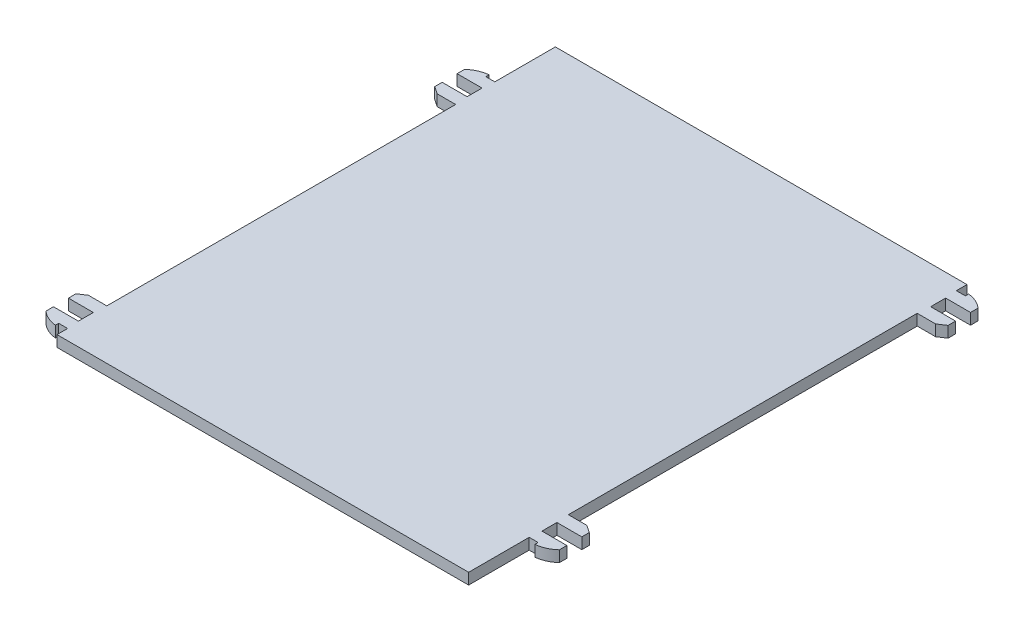
SolidWorks part; units mm, degrees
ref_plane "Front" through (0, 0, 0) normal (0, 0, 1) x (1, 0, 0)
ref_plane "Top" through (0, 0, 0) normal (0, 1, 0) x (1, 0, 0)
ref_plane "Right" through (0, 0, 0) normal (1, 0, 0) x (0, 0, -1)
sketch "Sketch1" plane through (0, 0, 0) normal (0, 1, 0) x (1, 0, 0)
  line L0 (43.1, 45.51) -> (46.5, 45.51)
  line L1 (-41.3, 50) -> (41.3, 50)
  line L2 (-41.3, 50) -> (-41.3, -50)
  line L3 (-41.3, -50) -> (41.3, -50)
  line L4 (41.3, 50) -> (41.3, -50)
  line L5 (-41.3, 50) -> (41.3, -50) construction
  line L6 (-41.3, -50) -> (41.3, 50) construction
  line L7 (41.3, 47.87) -> (43.1, 47.87)
  line L8 (41.3, 47.87) -> (41.3, 45.51)
  line L9 (41.3, 45.51) -> (43.1, 45.51)
  line L10 (43.1, 47.87) -> (43.1, 45.51)
  line L11 (46.5, 45.51) -> (46.5, 47.01)
  line L12 (43.1, 47.87) -> (43.1, 48.52)
  line L13 (41.3, 45.51) -> (41.5, 45.51)
  line L14 (41.3, 45.51) -> (41.3, 42.51)
  line L15 (41.3, 42.51) -> (41.5, 42.51)
  line L16 (41.5, 45.51) -> (41.5, 42.51)
  line L17 (41.5, 42.51) -> (46.5, 42.51)
  line L18 (46.5, 42.51) -> (46.5, 41.01)
  line L19 (46.5, 41.01) -> (45, 40.01)
  line L20 (45, 40.01) -> (41.3, 40.01)
  line L21 (41.3, 5.01) -> (60.4529, 5.01) construction
  line L22 (41.5, -32.49) -> (46.5, -32.49)
  line L23 (46.5, -32.49) -> (46.5, -30.99)
  line L24 (46.5, -30.99) -> (45, -29.99)
  line L25 (45, -29.99) -> (41.3, -29.99)
  line L26 (43.1, -37.85) -> (43.1, -38.5)
  line L27 (46.5, -35.49) -> (46.5, -36.99)
  line L28 (43.1, -35.49) -> (46.5, -35.49)
  line L29 (41.3, -35.49) -> (43.1, -35.49)
  line L30 (43.1, -37.85) -> (43.1, -35.49)
  line L31 (41.3, -37.85) -> (43.1, -37.85)
  line L32 (41.3, -37.85) -> (41.3, -35.49)
  line L33 (41.3, -32.49) -> (41.5, -32.49)
  line L34 (41.5, -35.49) -> (41.5, -32.49)
  line L35 (41.3, -35.49) -> (41.5, -35.49)
  line L36 (41.3, -35.49) -> (41.3, -32.49)
  line L37 (0, 36.7793) -> (0, -23.6766) construction
  line L38 (-41.3, -5.01) -> (-64.7336, -5.01) construction
  line L39 (-45, -40.01) -> (-41.3, -40.01)
  line L40 (-46.5, -41.01) -> (-45, -40.01)
  line L41 (-46.5, -42.51) -> (-46.5, -41.01)
  line L42 (-41.5, -42.51) -> (-46.5, -42.51)
  line L43 (-41.5, -45.51) -> (-41.5, -42.51)
  line L44 (-41.3, -45.51) -> (-46.5, -45.51)
  line L45 (-43.1, -47.87) -> (-41.3, -47.87)
  line L46 (-43.1, -47.87) -> (-43.1, -48.52)
  line L47 (-46.5, -45.51) -> (-46.5, -47.01)
  line L59 (-41.3, 47.87) -> (-41.3, 45.51)
  line L60 (-41.3, 47.87) -> (-41.3, 37.87) construction
  line L61 (-43.1, 37.85) -> (-41.3, 37.85)
  line L62 (-43.1, 37.85) -> (-43.1, 38.5)
  line L63 (-41.3, 35.49) -> (-46.5, 35.49)
  line L64 (-46.5, 35.49) -> (-46.5, 36.99)
  line L65 (-41.5, 35.49) -> (-41.5, 32.49)
  line L66 (-41.5, 32.49) -> (-46.5, 32.49)
  line L67 (-46.5, 32.49) -> (-46.5, 30.99)
  line L68 (-46.5, 30.99) -> (-45, 29.99)
  line L69 (-45, 29.99) -> (-41.3, 29.99)
  arc A0 (43.1, 48.52) -> (46.5, 47.01) centre (42.5287, 42.6507) cw
  arc A1 (43.1, -38.5) -> (46.5, -36.99) centre (42.5287, -32.6307) ccw
  arc A2 (-46.5, -47.01) -> (-43.1, -48.52) centre (-42.5287, -42.6507) ccw
  arc A4 (-46.5, 36.99) -> (-43.1, 38.5) centre (-42.5287, 32.6307) cw
  point P0 (0, 0)
  dimension "D9" = 0.65
  dimension "D10" = 5.897
  dimension "D25" = 5.897
  dimension "D1" = 82.6
  dimension "D2" = 100
  dimension "D3" = 2.13
  dimension "D4" = 2.36
  dimension "D5" = 1.8
  dimension "D6" = 0.2
  dimension "D7" = 5.2
  dimension "D8" = 1.5
  dimension "D11" = 3
  dimension "D12" = 1.5
  dimension "D13" = 3.7
  dimension "D14" = 2.5
  dimension "D15" = 5.2
  dimension "D16" = 35
  dimension "D17" = 10
  dimension "D18" = 5.2
  dimension "D19" = 1.8
  dimension "D20" = 1.5
  dimension "D21" = 12.15
  dimension "D22" = 2.36
  dimension "D23" = 0.2
  dimension "D24" = 0.65
  dimension "D26" = 1.5
  dimension "D27" = 2.5
  dimension "D28" = 3.7
  dimension "D29" = 5
  dimension "D30" = 3
  dimension "D31" = 35
  dimension "D32" = 2.13
extrude "Boss-Extrude1" add sketch "Sketch1" along normal blind 2.23 contours L26 A1 L27 L28 L30 | L4 L31 L30 L29 | L4 L33 L22 L23 L24 L25 | L29 L34 L33 L4 | L4 L1 L2 L3 | L20 L19 L18 L17 L15 L4 | L16 L9 L4 L15 | L10 L7 L4 L9 | A0 L12 L10 L0 L11 | L47 A2 L46 L45 L2 L44 | L44 L2 L39 L40 L41 L42 L43 | L68 L69 L2 L63 L65 L66 L67 | A4 L64 L63 L2 L61 L62
sketch "Sketch2" plane through (0, 2.23, 0) normal (0, 1, 0) x (1, 0, 0)
  line L0 (-41.3, -50) -> (41.3, -50) construction
  line L1 (-21.5, -43.75) -> (-28.9, -43.75)
  line L2 (-21.5, -43.75) -> (-21.5, -47.5)
  line L3 (-21.5, -47.5) -> (-28.9, -47.5)
  line L4 (-28.9, -43.75) -> (-28.9, -47.5)
  line L5 (-41.5, -45.51) -> (-41.5, -42.51) construction
  line L6 (0, -50) -> (0, -10.7982) construction
  line L7 (21.5, -43.75) -> (21.5, -47.5)
  line L8 (21.5, -47.5) -> (28.9, -47.5)
  line L9 (28.9, -43.75) -> (28.9, -47.5)
  line L10 (21.5, -43.75) -> (28.9, -43.75)
  point P10 (0, 0)
  dimension "D1" = 2.5
  dimension "D2" = 12.6
  dimension "D3" = 7.4
  dimension "D4" = 3.75
